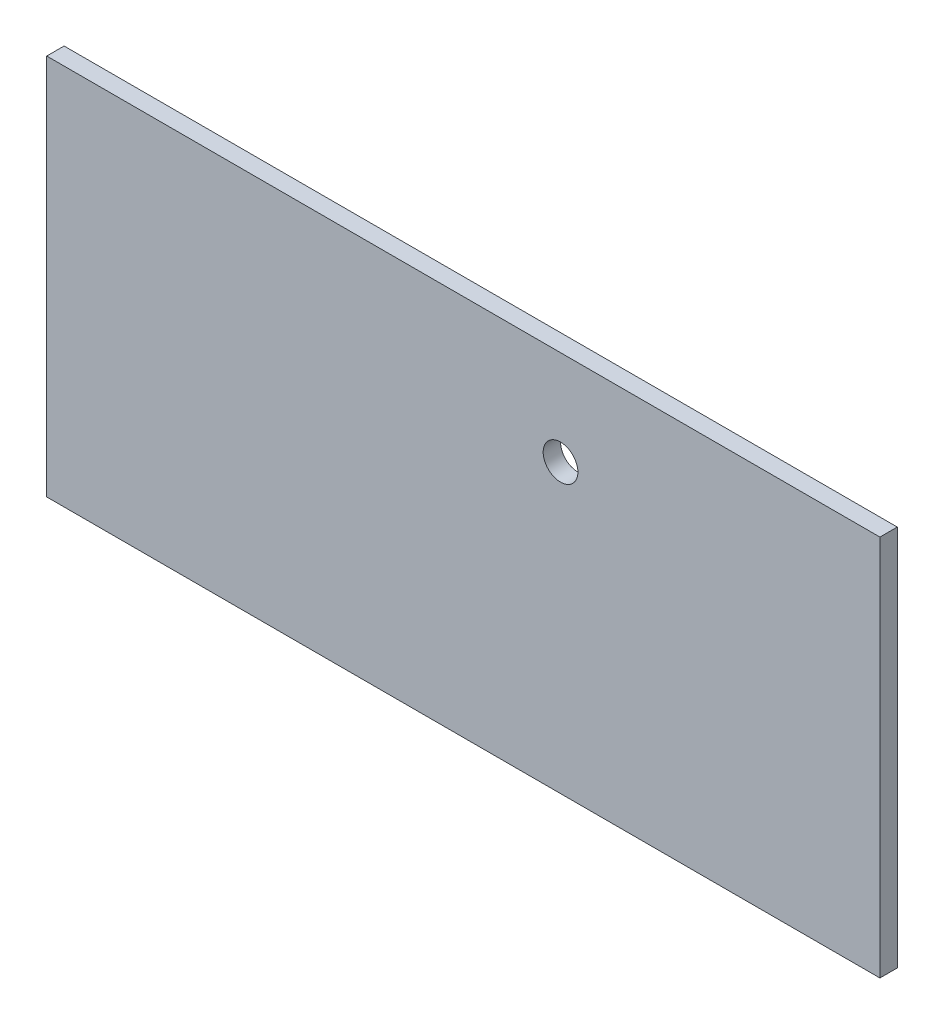
SolidWorks part; units mm, degrees
ref_plane "Plan de face" through (0, 0, 0) normal (0, 0, 1) x (1, 0, 0)
ref_plane "Plan de dessus" through (0, 0, 0) normal (0, 1, 0) x (1, 0, 0)
ref_plane "Plan de droite" through (0, 0, 0) normal (1, 0, 0) x (0, 0, -1)
sketch "Esquisse1" plane through (0, 0, 0) normal (0, 0, 1) x (1, 0, 0)
  line L1 (0, 0) -> (-240, 0)
  line L2 (0, 0) -> (0, 50)
  line L3 (0, 50) -> (-240, 50)
  line L4 (-240, 0) -> (-240, 50)
  dimension "D1" = 240
  dimension "D2" = 50
extrude "Boss.-Extru.1" add sketch "Esquisse1" along normal blind 5
sketch "Esquisse2" plane through (0, 50, 0) normal (0, 1, 0) x (1, 0, 0)
  line L1 (-240, -5) -> (0, -5)
  line L2 (-240, -5) -> (-240, 0)
  line L3 (-240, 0) -> (0, 0)
  line L4 (0, -5) -> (0, 0)
extrude "Boss.-Extru.2" add sketch "Esquisse2" along normal blind 50
sketch "Esquisse4" plane through (0, 0, 5) normal (0, 0, 1) x (1, 0, 0)
  line L0 (0, 0) -> (0, 100) construction
  line L2 (-240, 0) -> (0, 0) construction
  circle A0 centre (-186.6717, 79.9539) radius 12.7546
  circle A1 centre (-92, 82.7) radius 5
  dimension "D1" = 92
  dimension "D2" = 82.7
  dimension "D3" = 10
extrude "Enlèv. mat.-Extru.1" cut sketch "Esquisse4" against normal blind 5 contours A1
sketch "Esquisse5" plane through (0, 100, 0) normal (0, 1, 0) x (1, 0, 0)
  line L0 (0, 0) -> (-240, 0) construction
  line L1 (-240, 0) -> (0, 0)
  line L2 (-240, 0) -> (-240, -5)
  line L3 (-240, -5) -> (0, -5)
  line L4 (0, 0) -> (0, -5)
  line L5 (-240, 0) -> (-240, -5) construction
extrude "Boss.-Extru.3" add sketch "Esquisse5" along normal blind 10
